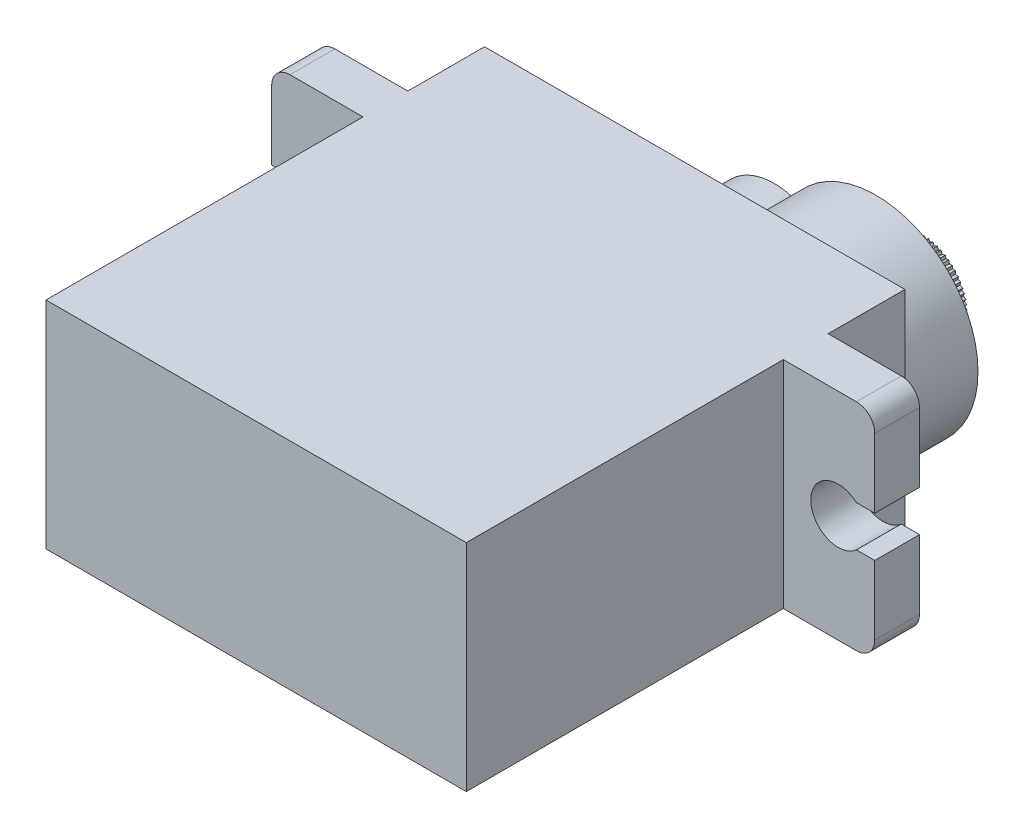
SolidWorks part; units mm, degrees
other "Markup1"
sketch "Sketch1" plane through (16.5, -6.05, -13.15) normal (0.2287, -0.9517, -0.2048) x (0.1643, 0.245, -0.9555)
ref_plane "Ön Düzlem" through (0, 0, 0) normal (0, 0, 1) x (1, 0, 0)
ref_plane "Üst Düzlem" through (0, 0, 0) normal (0, 1, 0) x (1, 0, 0)
ref_plane "Sağ Düzlem" through (0, 0, 0) normal (1, 0, 0) x (0, 0, -1)
sketch "Çizim1" plane through (0, 0, 0) normal (0, 0, 1) x (1, 0, 0)
  line L1 (-11.5, -5.9) -> (11.5, -5.9)
  line L2 (-11.5, -5.9) -> (-11.5, 5.9)
  line L3 (-11.5, 5.9) -> (11.5, 5.9)
  line L4 (11.5, -5.9) -> (11.5, 5.9)
  line L5 (-11.5, -5.9) -> (11.5, 5.9) construction
  line L6 (-11.5, 5.9) -> (11.5, -5.9) construction
  point P0 (0, 0)
  dimension "D1" = 23
  dimension "D2" = 11.8
extrude "Yükseklik-Ekstrüzyon1" add sketch "Çizim1" along normal blind 17.35
sketch "Çizim4" plane through (11.5, 0, 0) normal (1, 0, 0) x (0, 0, -1)
  line L0 (-17.35, -5.9) -> (0, -5.9) construction
  line L1 (0, 5.9) -> (2.45, 5.9)
  line L2 (0, 5.9) -> (0, -5.9)
  line L3 (0, -5.9) -> (2.45, -5.9)
  line L4 (2.45, 5.9) -> (2.45, -5.9)
  dimension "D1" = 2.45
extrude "Yükseklik-Ekstrüzyon2" add sketch "Çizim4" along normal blind 5
sketch "Çizim5" plane through (-11.5, 0, 0) normal (-1, 0, 0) x (0, 0, 1)
  line L0 (17.35, 5.9) -> (0, 5.9) construction
  line L1 (0, -5.9) -> (-2.45, -5.9)
  line L2 (0, -5.9) -> (0, 5.9)
  line L3 (0, 5.9) -> (-2.45, 5.9)
  line L4 (-2.45, -5.9) -> (-2.45, 5.9)
  dimension "D1" = 2.45
extrude "Yükseklik-Ekstrüzyon3" add sketch "Çizim5" along normal blind 5
sketch "Çizim6" plane through (16.5, 0, 0) normal (1, 0, 0) x (0, 0, -1)
  line L0 (0, 0) -> (2.45, 0) construction
  line L1 (0, 5.9) -> (0, -5.9) construction
  line L2 (2.45, -5.9) -> (2.45, 5.9) construction
  line L4 (2.45, 1.12) -> (0, 1.12)
  line L5 (2.45, 1.12) -> (2.45, -1.12)
  line L6 (2.45, -1.12) -> (0, -1.12)
  line L7 (0, 1.12) -> (0, -1.12)
  line L8 (2.45, 1.12) -> (0, -1.12) construction
  line L9 (2.45, -1.12) -> (0, 1.12) construction
  point P6 (1.225, 0)
  dimension "D1" = 2.24
sketch "Çizim7" plane through (0, 0, 0) normal (0, 0, -1) x (-1, 0, 0)
  line L0 (-11.5, 5.9) -> (11.5, 5.9) construction
  line L1 (-11.5, -5.9) -> (11.5, -5.9)
  line L2 (-11.5, -5.9) -> (-11.5, 5.9)
  line L3 (-11.5, 5.9) -> (11.5, 5.9)
  line L4 (11.5, -5.9) -> (11.5, 5.9)
  line L5 (-11.5, -5.9) -> (11.5, 5.9) construction
  line L6 (-11.5, 5.9) -> (11.5, -5.9) construction
  point P0 (0, 0)
  dimension "D1" = 23
extrude "Yükseklik-Ekstrüzyon4" add sketch "Çizim7" along normal blind 6.65
sketch "Çizim8" plane through (0, 0, -2.45) normal (0, 0, -1) x (-1, 0, 0)
  line L0 (0, 0.2404) -> (0, 3.5063) construction
  circle A0 centre (-14.5, 0) radius 1.5
  circle A1 centre (14.5, 0) radius 1.5
  dimension "D2" = 3
  dimension "D1" = 3
extrude "Kes-Ekstrüzyon1" cut sketch "Çizim8" against normal up to surface (2.45 mm away) up to face at (14, 0, 0)
fillet "Radyus1" radius 1 4 edges at (-16.5, 5.9, -1.225) (-16.5, -5.9, -1.225) (16.5, -5.9, -1.225) (16.5, 5.9, -1.225)
extrude "Kes-Ekstrüzyon2" cut sketch "Çizim6" against normal blind 1
sketch "Çizim9" plane through (-16.5, 0, 0) normal (-1, 0, 0) x (0, 0, 1)
  line L0 (0, 0) -> (-2.45, 0) construction
  line L1 (-2.45, 5.9) -> (-2.45, -5.9) construction
  line L2 (0, -5.9) -> (0, 5.9) construction
  line L3 (-2.45, -1.12) -> (0, -1.12)
  line L4 (-2.45, -1.12) -> (-2.45, 1.12)
  line L5 (-2.45, 1.12) -> (0, 1.12)
  line L6 (0, -1.12) -> (0, 1.12)
  line L7 (-2.45, -1.12) -> (0, 1.12) construction
  line L8 (-2.45, 1.12) -> (0, -1.12) construction
  point P5 (-1.225, 0)
  dimension "D1" = 2.24
extrude "Kes-Ekstrüzyon3" cut sketch "Çizim9" against normal blind 1
sketch "Çizim10" plane through (0, 0, -6.65) normal (0, 0, -1) x (-1, 0, 0)
  line L0 (-11.5, 0) -> (-5.925, 0) construction
  line L1 (-11.5, 5.9) -> (-11.5, -5.9) construction
  circle A0 centre (-5.925, 0) radius 5.575
  dimension "D2" = 11.15
  dimension "D1" = 5.575
extrude "Yükseklik-Ekstrüzyon5" add sketch "Çizim10" along normal blind 4
sketch "Çizim11" plane through (0, 0, -10.65) normal (0, 0, -1) x (-1, 0, 0)
  circle A0 centre (-5.925, 0) radius 2.5
  dimension "D1" = 5
extrude "Yükseklik-Ekstrüzyon6" add sketch "Çizim11" along normal blind 2.5
sketch "Çizim12" plane through (0, 0, -6.65) normal (0, 0, -1) x (-1, 0, 0)
  line L0 (-0.35, 0) -> (3, 0) construction
  circle A0 centre (-5.925, 0) radius 5.575 construction
  circle A1 centre (-5.925, 0) radius 5.575 construction
  circle A2 centre (-0.35, 0) radius 3.35
  dimension "D1" = 3.35
extrude "Yükseklik-Ekstrüzyon7" add sketch "Çizim12" along normal blind 4
sketch "Çizim13" plane through (0, 0, -13.15) normal (0, 0, -1) x (-1, 0, 0)
  line L0 (-5.925, 2.375) -> (-5.815, 2.485)
  line L1 (-5.925, 2.375) -> (-6.035, 2.485)
  line L2 (-6.035, 2.485) -> (-6.1562, 2.3637)
  line L3 (-5.815, 2.485) -> (-5.6938, 2.3637)
  line L4 (-5.5481, 2.4587) -> (-5.6906, 2.3634)
  line L5 (-5.4617, 2.3294) -> (-5.5481, 2.4587)
  line L6 (-5.4617, 2.3294) -> (-5.3324, 2.4158)
  line L7 (-5.3324, 2.4158) -> (-5.2371, 2.2732)
  line L8 (-5.0756, 2.3379) -> (-5.234, 2.2723)
  line L9 (-5.0161, 2.1942) -> (-5.0756, 2.3379)
  line L10 (-5.0161, 2.1942) -> (-4.8725, 2.2537)
  line L11 (-4.8725, 2.2537) -> (-4.8068, 2.0953)
  line L12 (-4.6359, 2.1273) -> (-4.804, 2.0938)
  line L13 (-4.6055, 1.9747) -> (-4.6359, 2.1273)
  line L14 (-4.6055, 1.9747) -> (-4.453, 2.0051)
  line L15 (-4.453, 2.0051) -> (-4.4196, 1.8369)
  line L16 (-4.2456, 1.8349) -> (-4.4171, 1.8349)
  line L17 (-4.2456, 1.6794) -> (-4.2456, 1.8349)
  line L18 (-4.2456, 1.6794) -> (-4.0901, 1.6794)
  line L19 (-4.0901, 1.6794) -> (-4.0901, 1.5079)
  line L20 (-3.9199, 1.472) -> (-4.0881, 1.5054)
  line L21 (-3.9503, 1.3195) -> (-3.9199, 1.472)
  line L22 (-3.9503, 1.3195) -> (-3.7977, 1.2891)
  line L23 (-3.7977, 1.2891) -> (-3.8312, 1.121)
  line L24 (-3.6713, 1.0525) -> (-3.8297, 1.1182)
  line L25 (-3.7308, 0.9089) -> (-3.6713, 1.0525)
  line L26 (-3.7308, 0.9089) -> (-3.5871, 0.8494)
  line L27 (-3.5871, 0.8494) -> (-3.6527, 0.691)
  line L28 (-3.5092, 0.5926) -> (-3.6518, 0.6879)
  line L29 (-3.5956, 0.4633) -> (-3.5092, 0.5926)
  line L30 (-3.5956, 0.4633) -> (-3.4663, 0.3769)
  line L31 (-3.4663, 0.3769) -> (-3.5616, 0.2344)
  line L32 (-3.44, 0.11) -> (-3.5613, 0.2312)
  line L33 (-3.55, 0) -> (-3.44, 0.11)
  line L34 (-3.55, 0) -> (-3.44, -0.11)
  line L35 (-3.44, -0.11) -> (-3.5613, -0.2312)
  line L36 (-3.4663, -0.3769) -> (-3.5616, -0.2344)
  line L37 (-3.5956, -0.4633) -> (-3.4663, -0.3769)
  line L38 (-3.5956, -0.4633) -> (-3.5092, -0.5926)
  line L39 (-3.5092, -0.5926) -> (-3.6518, -0.6879)
  line L40 (-3.5871, -0.8494) -> (-3.6527, -0.691)
  line L41 (-3.7308, -0.9089) -> (-3.5871, -0.8494)
  line L42 (-3.7308, -0.9089) -> (-3.6713, -1.0525)
  line L43 (-3.6713, -1.0525) -> (-3.8297, -1.1182)
  line L44 (-3.7977, -1.2891) -> (-3.8312, -1.121)
  line L45 (-3.9503, -1.3195) -> (-3.7977, -1.2891)
  line L46 (-3.9503, -1.3195) -> (-3.9199, -1.472)
  line L47 (-3.9199, -1.472) -> (-4.0881, -1.5054)
  line L48 (-4.0901, -1.6794) -> (-4.0901, -1.5079)
  line L49 (-4.2456, -1.6794) -> (-4.0901, -1.6794)
  line L50 (-4.2456, -1.6794) -> (-4.2456, -1.8349)
  line L51 (-4.2456, -1.8349) -> (-4.4171, -1.8349)
  line L52 (-4.453, -2.0051) -> (-4.4196, -1.8369)
  line L53 (-4.6055, -1.9747) -> (-4.453, -2.0051)
  line L54 (-4.6055, -1.9747) -> (-4.6359, -2.1273)
  line L55 (-4.6359, -2.1273) -> (-4.804, -2.0938)
  line L56 (-4.8725, -2.2537) -> (-4.8068, -2.0953)
  line L57 (-5.0161, -2.1942) -> (-4.8725, -2.2537)
  line L58 (-5.0161, -2.1942) -> (-5.0756, -2.3379)
  line L59 (-5.0756, -2.3379) -> (-5.234, -2.2723)
  line L60 (-5.3324, -2.4158) -> (-5.2371, -2.2732)
  line L61 (-5.4617, -2.3294) -> (-5.3324, -2.4158)
  line L62 (-5.4617, -2.3294) -> (-5.5481, -2.4587)
  line L63 (-5.5481, -2.4587) -> (-5.6906, -2.3634)
  line L64 (-5.815, -2.485) -> (-5.6938, -2.3637)
  line L65 (-5.925, -2.375) -> (-5.815, -2.485)
  line L66 (-5.925, -2.375) -> (-6.035, -2.485)
  line L67 (-6.035, -2.485) -> (-6.1562, -2.3637)
  line L68 (-6.3019, -2.4587) -> (-6.1594, -2.3634)
  line L69 (-6.3883, -2.3294) -> (-6.3019, -2.4587)
  line L70 (-6.3883, -2.3294) -> (-6.5176, -2.4158)
  line L71 (-6.5176, -2.4158) -> (-6.6129, -2.2732)
  line L72 (-6.7744, -2.3379) -> (-6.616, -2.2723)
  line L73 (-6.8339, -2.1942) -> (-6.7744, -2.3379)
  line L74 (-6.8339, -2.1942) -> (-6.9775, -2.2537)
  line L75 (-6.9775, -2.2537) -> (-7.0432, -2.0953)
  line L76 (-7.2141, -2.1273) -> (-7.046, -2.0938)
  line L77 (-7.2445, -1.9747) -> (-7.2141, -2.1273)
  line L78 (-7.2445, -1.9747) -> (-7.397, -2.0051)
  line L79 (-7.397, -2.0051) -> (-7.4304, -1.8369)
  line L80 (-7.6044, -1.8349) -> (-7.4329, -1.8349)
  line L81 (-7.6044, -1.6794) -> (-7.6044, -1.8349)
  line L82 (-7.6044, -1.6794) -> (-7.7599, -1.6794)
  line L83 (-7.7599, -1.6794) -> (-7.7599, -1.5079)
  line L84 (-7.9301, -1.472) -> (-7.7619, -1.5054)
  line L85 (-7.8997, -1.3195) -> (-7.9301, -1.472)
  line L86 (-7.8997, -1.3195) -> (-8.0523, -1.2891)
  line L87 (-8.0523, -1.2891) -> (-8.0188, -1.121)
  line L88 (-8.1787, -1.0525) -> (-8.0203, -1.1182)
  line L89 (-8.1192, -0.9089) -> (-8.1787, -1.0525)
  line L90 (-8.1192, -0.9089) -> (-8.2629, -0.8494)
  line L91 (-8.2629, -0.8494) -> (-8.1973, -0.691)
  line L92 (-8.3408, -0.5926) -> (-8.1982, -0.6879)
  line L93 (-8.2544, -0.4633) -> (-8.3408, -0.5926)
  line L94 (-8.2544, -0.4633) -> (-8.3837, -0.3769)
  line L95 (-8.3837, -0.3769) -> (-8.2884, -0.2344)
  line L96 (-8.41, -0.11) -> (-8.2887, -0.2312)
  line L97 (-8.3, 0) -> (-8.41, -0.11)
  line L98 (-8.3, 0) -> (-8.41, 0.11)
  line L99 (-8.41, 0.11) -> (-8.2887, 0.2312)
  line L100 (-8.3837, 0.3769) -> (-8.2884, 0.2344)
  line L101 (-8.2544, 0.4633) -> (-8.3837, 0.3769)
  line L102 (-8.2544, 0.4633) -> (-8.3408, 0.5926)
  line L103 (-8.3408, 0.5926) -> (-8.1982, 0.6879)
  line L104 (-8.2629, 0.8494) -> (-8.1973, 0.691)
  line L105 (-8.1192, 0.9089) -> (-8.2629, 0.8494)
  line L106 (-8.1192, 0.9089) -> (-8.1787, 1.0525)
  line L107 (-8.1787, 1.0525) -> (-8.0203, 1.1182)
  line L108 (-8.0523, 1.2891) -> (-8.0188, 1.121)
  line L109 (-7.8997, 1.3195) -> (-8.0523, 1.2891)
  line L110 (-7.8997, 1.3195) -> (-7.9301, 1.472)
  line L111 (-7.9301, 1.472) -> (-7.7619, 1.5054)
  line L112 (-7.7599, 1.6794) -> (-7.7599, 1.5079)
  line L113 (-7.6044, 1.6794) -> (-7.7599, 1.6794)
  line L114 (-7.6044, 1.6794) -> (-7.6044, 1.8349)
  line L115 (-7.6044, 1.8349) -> (-7.4329, 1.8349)
  line L116 (-7.397, 2.0051) -> (-7.4304, 1.8369)
  line L117 (-7.2445, 1.9747) -> (-7.397, 2.0051)
  line L118 (-7.2445, 1.9747) -> (-7.2141, 2.1273)
  line L119 (-7.2141, 2.1273) -> (-7.046, 2.0938)
  line L120 (-6.9775, 2.2537) -> (-7.0432, 2.0953)
  line L121 (-6.8339, 2.1942) -> (-6.9775, 2.2537)
  line L122 (-6.8339, 2.1942) -> (-6.7744, 2.3379)
  line L123 (-6.7744, 2.3379) -> (-6.616, 2.2723)
  line L124 (-6.5176, 2.4158) -> (-6.6129, 2.2732)
  line L125 (-6.3883, 2.3294) -> (-6.5176, 2.4158)
  line L126 (-6.3883, 2.3294) -> (-6.3019, 2.4587)
  line L127 (-6.3019, 2.4587) -> (-6.1594, 2.3634)
  line L128 (-8.1973, 0.691) -> (-8.1982, 0.6879)
  line L129 (-8.0188, 1.121) -> (-8.0203, 1.1182)
  line L130 (-7.7599, 1.5079) -> (-7.7619, 1.5054)
  line L131 (-7.4304, 1.8369) -> (-7.4329, 1.8349)
  line L132 (-7.0432, 2.0953) -> (-7.046, 2.0938)
  line L133 (-6.6129, 2.2732) -> (-6.616, 2.2723)
  line L134 (-6.1562, 2.3637) -> (-6.1594, 2.3634)
  line L135 (-5.6906, 2.3634) -> (-5.6938, 2.3637)
  line L136 (-5.234, 2.2723) -> (-5.2371, 2.2732)
  line L137 (-4.804, 2.0938) -> (-4.8068, 2.0953)
  line L138 (-4.4171, 1.8349) -> (-4.4196, 1.8369)
  line L139 (-4.0881, 1.5054) -> (-4.0901, 1.5079)
  line L140 (-3.8297, 1.1182) -> (-3.8312, 1.121)
  line L141 (-3.6518, 0.6879) -> (-3.6527, 0.691)
  line L142 (-3.5613, 0.2312) -> (-3.5616, 0.2344)
  line L143 (-3.5616, -0.2344) -> (-3.5613, -0.2312)
  line L144 (-3.6527, -0.691) -> (-3.6518, -0.6879)
  line L145 (-3.8312, -1.121) -> (-3.8297, -1.1182)
  line L146 (-4.0901, -1.5079) -> (-4.0881, -1.5054)
  line L147 (-4.4196, -1.8369) -> (-4.4171, -1.8349)
  line L148 (-4.8068, -2.0953) -> (-4.804, -2.0938)
  line L149 (-5.2371, -2.2732) -> (-5.234, -2.2723)
  line L150 (-5.6938, -2.3637) -> (-5.6906, -2.3634)
  line L151 (-6.1594, -2.3634) -> (-6.1562, -2.3637)
  line L152 (-6.616, -2.2723) -> (-6.6129, -2.2732)
  line L153 (-7.046, -2.0938) -> (-7.0432, -2.0953)
  line L154 (-7.4329, -1.8349) -> (-7.4304, -1.8369)
  line L155 (-7.7619, -1.5054) -> (-7.7599, -1.5079)
  line L156 (-8.0203, -1.1182) -> (-8.0188, -1.121)
  line L157 (-8.1982, -0.6879) -> (-8.1973, -0.691)
  line L158 (-8.2887, -0.2312) -> (-8.2884, -0.2344)
  line L159 (-8.2884, 0.2344) -> (-8.2887, 0.2312)
  circle A1 centre (-5.925, 0) radius 2.5
  point P167 (-5.925, 0)
  point P229 (-5.925, 0)
  dimension "D1" = 32
  dimension "D2" = 32
extrude "Kes-Ekstrüzyon4" cut sketch "Çizim13" against normal up to surface (2.5 mm away) up to face at (3.425, 0, -10.65)
sketch "Çizim14" plane through (0, 0, -13.15) normal (0, 0, -1) x (-1, 0, 0)
  line L0 (-11.5, 0) -> (-5.925, 0) construction
  line L1 (-11.5, -5.9) -> (-11.5, 5.9) construction
  circle A0 centre (-5.925, 0) radius 0.75
  dimension "D1" = 1.5
extrude "Kes-Ekstrüzyon5" cut sketch "Çizim14" against normal blind 1
sketch "Çizim15" plane through (0, -5.9, 0) normal (0, -1, 0) x (1, 0, 0)
  line L0 (0, 17.35) -> (0, 15.35) construction
  line L1 (-11.5, 17.35) -> (11.5, 17.35) construction
  line L2 (-11.5, 8.675) -> (-9.5, 8.675) construction
  line L3 (-11.5, 17.35) -> (-11.5, 0) construction
  line L4 (11.5, 17.35) -> (11.5, 0) construction
  line L5 (-9.5, 15.35) -> (9.5, 15.35)
  line L6 (-9.5, 15.35) -> (-9.5, 2)
  line L7 (-9.5, 2) -> (9.5, 2)
  line L8 (9.5, 15.35) -> (9.5, 2)
  dimension "D1" = 2
  dimension "D2" = 2
  dimension "D3" = 2
  dimension "D4" = 2
  dimension "D5" = 2
extrude "Yükseklik-Ekstrüzyon8" add sketch "Çizim15" along normal blind 0.1
sketch "Çizim16" plane through (0, -6, 0) normal (0, -1, 0) x (1, 0, 0)
  line L0 (0, 2) -> (0, 5) construction
  line L1 (-9.5, 2) -> (9.5, 2) construction
  line L2 (9, 5) -> (-9, 5) construction
  text T0 "TOWER PRO" font "Century Gothic" height 2
  point P8 (0, 5)
extrude "Kes-Ekstrüzyon6" cut sketch "Çizim16" against normal blind 0.1
sketch "Çizim17" plane through (0, -6, 0) normal (0, -1, 0) x (1, 0, 0)
  line L0 (-9.5, 8.675) -> (9.5, 8.675) construction
  line L1 (-9.5, 15.35) -> (-9.5, 2) construction
  line L2 (9.5, 2) -> (9.5, 15.35) construction
  line L4 (-9.5, 6.925) -> (9.5, 6.925)
  line L5 (-9.5, 6.925) -> (-9.5, 10.425)
  line L6 (-9.5, 10.425) -> (9.5, 10.425)
  line L7 (9.5, 6.925) -> (9.5, 10.425)
  line L8 (-9.5, 6.925) -> (9.5, 10.425) construction
  line L9 (-9.5, 10.425) -> (9.5, 6.925) construction
  point P6 (0, 8.675)
  dimension "D1" = 3.5
extrude "Yükseklik-Ekstrüzyon9" add sketch "Çizim17" along normal blind 0.05
sketch "Çizim18" plane through (0, -6.05, 0) normal (0, -1, 0) x (1, 0, 0)
  line L0 (-9.5, 8.675) -> (9.5, 8.675) construction
  line L1 (-9.5, 10.425) -> (-9.5, 6.925) construction
  line L2 (9.5, 6.925) -> (9.5, 10.425) construction
  line L3 (9.5, 8.675) -> (9.5, 10.425) construction
  line L4 (9.5, 2) -> (9.5, 15.35) construction
  line L5 (9.5, 9.55) -> (-9.5, 9.55) construction
  text T0 "MİCRO SERVO" font "Century Gothic" height 1
  text T1 "90" font "Century Gothic" height 0.6
extrude "Kes-Ekstrüzyon7" cut sketch "Çizim18" against normal blind 0.05
sketch "Çizim19" plane through (0, -6, 0) normal (0, -1, 0) x (1, 0, 0)
  line L0 (9.5, 12.8875) -> (-9.5, 12.8875) construction
  line L1 (9.5, 10.425) -> (9.5, 15.35) construction
  line L2 (-9.5, 15.35) -> (-9.5, 10.425) construction
  text T0 "SG90" font "Century Gothic" height 1.5
extrude "Kes-Ekstrüzyon8" cut sketch "Çizim19" against normal blind 0.1
sketch "Çizim21" plane through (0, -5.9, 0) normal (0, -1, 0) x (1, 0, 0)
  line L11 (-9.5, 2) -> (9.5, 2) construction
  line L12 (9.5, 2) -> (9.5, 15.35) construction
  line L13 (-9.5, 15.35) -> (-9.5, 2) construction
  line L14 (9.5, 15.35) -> (-9.5, 15.35) construction
  line L15 (-9.75, 1.75) -> (9.75, 1.75)
  line L16 (9.75, 1.75) -> (9.75, 15.6)
  line L17 (-9.75, 15.6) -> (-9.75, 1.75)
  line L18 (9.75, 15.6) -> (-9.75, 15.6)
  line L19 (-9.75, 1.75) -> (9.75, 1.75)
  line L20 (9.75, 1.75) -> (9.75, 15.6)
  line L21 (-9.75, 15.6) -> (-9.75, 1.75)
  line L22 (9.75, 15.6) -> (-9.75, 15.6)
  line L23 (-9.5, 2) -> (9.5, 2)
  line L24 (9.5, 2) -> (9.5, 15.35)
  line L25 (-9.5, 15.35) -> (-9.5, 2)
  line L26 (9.5, 15.35) -> (-9.5, 15.35)
  dimension "D1" = 0.25
extrude "Yükseklik-Ekstrüzyon10" add sketch "Çizim21" along normal blind 0.11
sketch "Çizim22" plane through (0, -5.9, 0) normal (0, -1, 0) x (1, 0, 0)
  line L0 (-9.75, 1.75) -> (9.75, 1.75) construction
  line L1 (9.75, 1.75) -> (9.75, 15.6) construction
  line L2 (9.75, 15.6) -> (-9.75, 15.6) construction
  line L3 (-9.75, 15.6) -> (-9.75, 1.75) construction
  line L4 (-9.75, 1.75) -> (9.75, 1.75)
  line L5 (9.75, 1.75) -> (9.75, 15.6)
  line L6 (9.75, 15.6) -> (-9.75, 15.6)
  line L7 (-9.75, 15.6) -> (-9.75, 1.75)
  line L8 (10, 15.85) -> (-10, 15.85)
  line L9 (-10, 15.85) -> (-10, 1.5)
  line L10 (-10, 1.5) -> (10, 1.5)
  line L11 (10, 1.5) -> (10, 15.85)
  dimension "D1" = 0.25
extrude "Yükseklik-Ekstrüzyon11" add sketch "Çizim22" along normal blind 0.1
